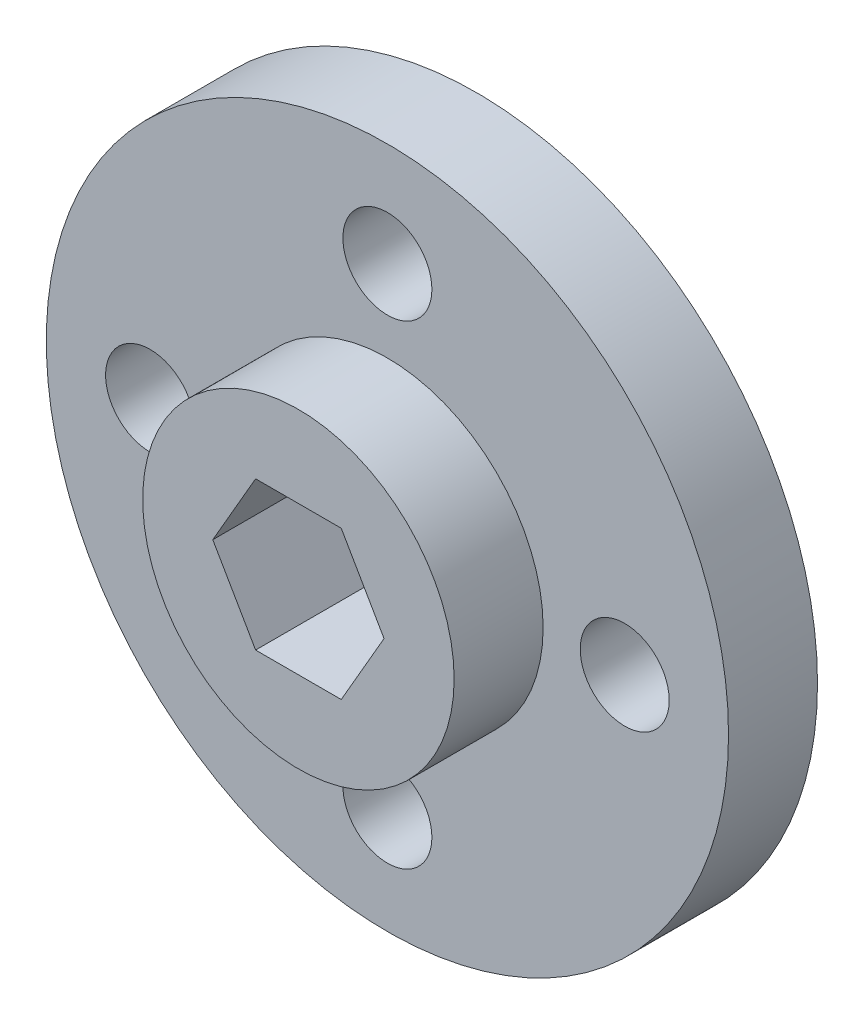
SolidWorks part; units mm, degrees
ref_plane "前基準面" through (0, 0, 0) normal (0, 0, 1) x (1, 0, 0)
ref_plane "上基準面" through (0, 0, 0) normal (0, 1, 0) x (1, 0, 0)
ref_plane "右基準面" through (0, 0, 0) normal (1, 0, 0) x (0, 0, -1)
sketch "草圖1" plane through (0, 0, 0) normal (0, 0, 1) x (1, 0, 0)
  circle A0 centre (0, 0) radius 11.5
  circle A1 centre (0, 0) radius 8 construction
  circle A2 centre (0, 8) radius 1.5
  circle A3 centre (8, 0) radius 1.5
  circle A4 centre (0, -8) radius 1.5
  circle A5 centre (-8, 0) radius 1.5
  point P6 (0, 0)
  point P7 (0, 0)
  dimension "D1" = 23
  dimension "D2" = 16
  dimension "D3" = 3
  dimension "D5" = 8
  dimension "D4" = 4
extrude "填料-伸長1" add sketch "草圖1" along normal blind 3
sketch "草圖2" plane through (0, 0, 3) normal (0, 0, 1) x (1, 0, 0)
  circle A0 centre (0, 0) radius 5.25
  dimension "D1" = 10.5
extrude "填料-伸長2" add sketch "草圖2" along normal blind 3
sketch "草圖3" plane through (0, 0, 6) normal (0, 0, 1) x (1, 0, 0)
  line L1 (2.8868, 0) -> (1.4434, 2.5)
  line L2 (1.4434, 2.5) -> (-1.4434, 2.5)
  line L3 (-1.4434, 2.5) -> (-2.8868, 0)
  line L4 (-2.8868, 0) -> (-1.4434, -2.5)
  line L5 (-1.4434, -2.5) -> (1.4434, -2.5)
  line L6 (1.4434, -2.5) -> (2.8868, 0)
  circle A0 centre (0, 0) radius 2.5 construction
  point P1 (0, 0)
  point P10 (2.8452, -0.4878)
  dimension "D1" = 5
extrude "除料-伸長1" cut sketch "草圖3" against normal blind 4.5
sketch "草圖4" plane through (0, 0, 1.5) normal (0, 0, 1) x (1, 0, 0)
  circle A0 centre (0, 0) radius 1.65
  dimension "D1" = 3.3
extrude "除料-伸長2" cut sketch "草圖4" against normal up to next
